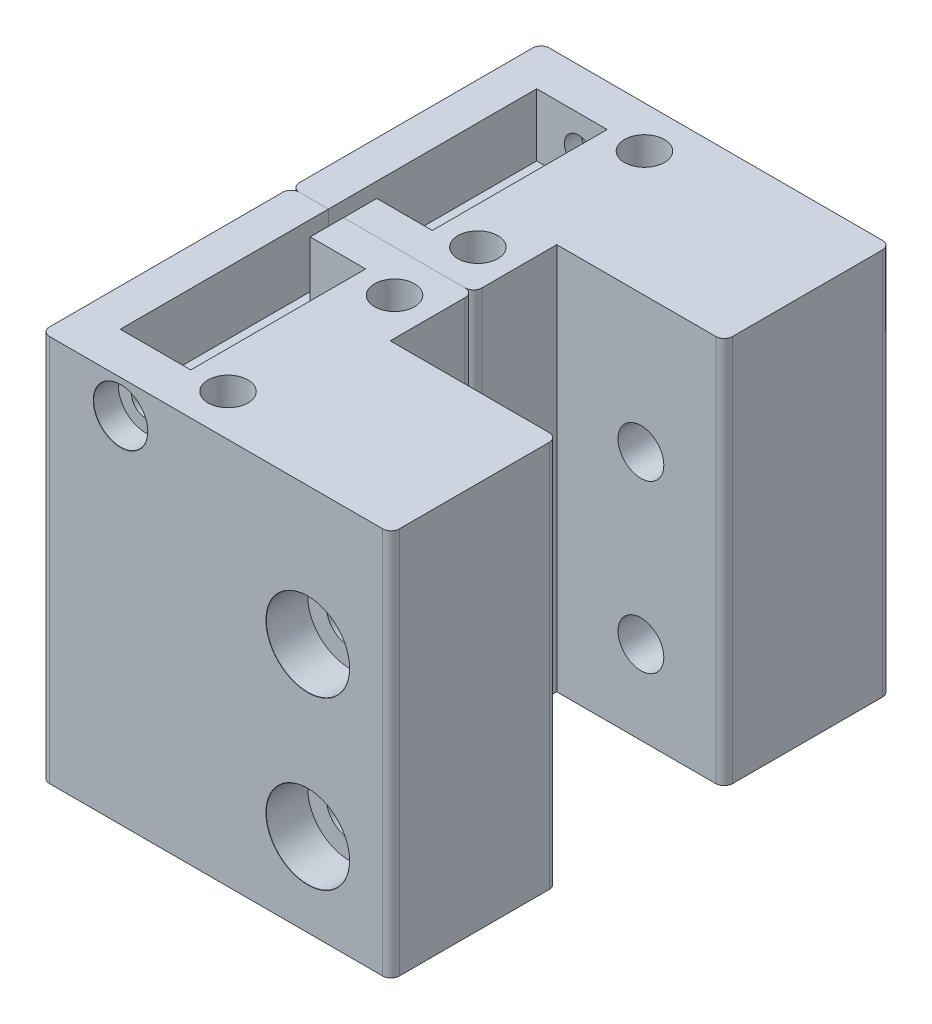
SolidWorks part; units mm, degrees
ref_plane "Front Plane" through (0, 0, 0) normal (0, 0, 1) x (1, 0, 0)
ref_plane "Top Plane" through (0, 0, 0) normal (0, 1, 0) x (1, 0, 0)
ref_plane "Right Plane" through (0, 0, 0) normal (1, 0, 0) x (0, 0, -1)
sketch "Sketch1" plane through (0, 0, 0) normal (0, 1, 0) x (1, 0, 0)
  line L1 (21, 10) -> (-21, 10)
  line L2 (21, 10) -> (21, -10)
  line L3 (21, -10) -> (-21, -10)
  line L4 (-21, 10) -> (-21, -10)
  line L5 (21, 10) -> (-21, -10) construction
  line L6 (21, -10) -> (-21, 10) construction
  point P0 (0, 0)
  dimension "D1" = 20
  dimension "D2" = 42
extrude "Boss-Extrude1" add sketch "Sketch1" along normal blind 40
sketch "Sketch2" plane through (0, 0, 10) normal (0, 0, 1) x (1, 0, 0)
  line L0 (21, 20) -> (-21, 20) construction
  line L3 (21, 40) -> (21, 0) construction
  line L4 (-21, 40) -> (-21, 0) construction
  line L5 (11, 30) -> (11, 10)
  point P9 (11, 20)
  dimension "D1" = 20
  dimension "D2" = 10
hole_wizard "CBORE for M5 SHCS1" positions "Sketch3" profile "Sketch4" counterbore size "M5" standard "ANSI Metric" end condition through all
sketch "Sketch3" plane through (0, 0, 10) normal (0, 0, 1) x (1, 0, 0)
  point P0 (11, 30)
  point P3 (11, 10)
sketch "Sketch4" plane through (11, 30, 10) normal (1, 0, 0) x (0, -1, 0)
  line L0 (0, 0) -> (0, 20)
  line L1 (0, 20) -> (2.75, 20)
  line L3 (2.75, 20) -> (2.75, 5)
  line L4 (5, 5) -> (2.75, 5)
  line L5 (5, 5) -> (5, 0.021)
  line L6 (5, 0.021) -> (5.025, 0)
  line L7 (5.025, 0) -> (0, 0)
  line L8 (-5, 0.021) -> (-5.025, 0) construction
  line L11 (0, -6.35) -> (0, 107.95) construction
  dimension "Thru Hole Dia." = 5.5
  dimension "Thru Hole Depth" = 20
  dimension "C'Bore Dia." = 10
  dimension "C'Bore Depth" = 5
  dimension "Near C'Sink Dia." = 10.05
  dimension "Near C'Sink Angle" = 100
sketch "Sketch5" plane through (0, 40, 0) normal (0, 1, 0) x (1, 0, 0)
  line L4 (-21, 10) -> (-21, -10)
  line L5 (-21, -10) -> (21, -10)
  line L6 (21, -10) -> (21, 10)
  line L7 (21, 10) -> (-21, 10)
  line L8 (-21, 10) -> (-21, -10)
  line L9 (-21, -10) -> (21, -10)
  line L10 (21, -10) -> (21, 10)
  line L11 (21, 10) -> (-21, 10)
  dimension "D1" = 0
extrude "Boss-Extrude2" add sketch "Sketch5" along normal blind 6.5
sketch "Sketch12" plane through (0, 46.5, 0) normal (0, 1, 0) x (1, 0, 0)
  line L0 (21, -10) -> (21, 10) construction
  line L1 (-21, 10) -> (0.9, 10)
  line L2 (-21, 10) -> (-21, 20)
  line L3 (-21, 20) -> (0.9, 20)
  line L4 (0.9, 10) -> (0.9, 20)
  dimension "D1" = 10
  dimension "D2" = 20.1
extrude "Boss-Extrude3" add sketch "Sketch12" against normal up to surface (46.5 mm away) up to face at (0, 0, 0)
sketch "Sketch6" plane through (0, 46.5, 0) normal (0, 1, 0) x (1, 0, 0)
  line L0 (-16.51, 20) -> (-16.51, -5)
  line L2 (-16.51, -5) -> (-8.05, -5)
  line L3 (-8.05, -5) -> (-8.05, 16)
  line L4 (-8.05, 16) -> (-14.71, 16)
  line L5 (-14.71, 16) -> (-14.71, 20)
  line L6 (-21, 20) -> (-21, -10) construction
  line L7 (-16.51, 20) -> (-14.71, 20)
  line L8 (21, -10) -> (-21, -10) construction
  line L9 (0.9, 20) -> (-21, 20) construction
  dimension "D1" = 4.49
  dimension "D2" = 1.8
  dimension "D3" = 5
  dimension "D4" = 8.46
  dimension "D5" = 4
extrude "Cut-Extrude1" cut sketch "Sketch6" against normal blind 7.5
fillet "Fillet1" radius 1 5 edges at (0.9, 23.25, -20) (21, 23.25, 10) (-21, 23.25, -20) (-21, 23.25, 10) (21, 23.25, -10)
sketch "Sketch7" plane through (0, 0, 10) normal (0, 0, 1) x (1, 0, 0)
  circle A0 centre (-11.48, 42.5) radius 1.65 construction
  circle A1 centre (-11.48, 42.5) radius 1.65
hole_wizard "CBORE for M3 SHCS1" positions "Sketch10" profile "Sketch11" counterbore size "M3" standard "ANSI Metric"
sketch "Sketch10" plane through (0, 0, 10) normal (0, 0, 1) x (1, 0, 0)
  point P0 (-11.48, 42.5)
sketch "Sketch11" plane through (-11.48, 42.5, 10) normal (1, 0, 0) x (0, -1, 0)
  line L0 (0, 0) -> (0, 6.0215)
  line L1 (0, 6.0215) -> (1.7, 5)
  line L2 (1.7, 5) -> (1.7, 3)
  line L3 (1.7, 3) -> (3.25, 3)
  line L5 (3.25, 3) -> (3.25, 0.021)
  line L6 (3.25, 0.021) -> (3.275, 0)
  line L7 (3.275, 0) -> (0, 0)
  line L8 (-3.25, 0.021) -> (-3.275, 0) construction
  line L10 (0, 6.0215) -> (-1.7, 5) construction
  line L11 (0, -6.35) -> (0, 107.95) construction
  dimension "Hole Dia." = 3.4
  dimension "Hole Depth" = 5
  dimension "C'Bore Dia." = 6.5
  dimension "C'Bore Depth" = 3
  dimension "Near C'Sink Dia." = 6.55
  dimension "Near C'Sink Angle" = 100
  dimension "Drill Angle" = 118
sketch "Sketch14" plane through (0, 46.5, 0) normal (0, 1, 0) x (1, 0, 0)
  line L0 (-3.575, 20) -> (-3.575, -10) construction
  line L1 (-0.1, 20) -> (-14.71, 20) construction
  line L2 (-20, -10) -> (20, -10) construction
  line L3 (0.9, 10) -> (0.9, 19) construction
  line L4 (-3.575, 15) -> (-3.575, -5) construction
  circle A0 centre (-3.575, 15) radius 2.4
  circle A1 centre (-3.575, -5) radius 2.4
  point P12 (-3.575, 5)
  dimension "D3" = 4.8
  dimension "D1" = 4.475
  dimension "D2" = 20
extrude "Cut-Extrude2" cut sketch "Sketch14" against normal blind 3.8
sketch "Sketch15" plane through (0, 42.7, 0) normal (0, 1, 0) x (1, 0, 0)
  circle A0 centre (-3.575, 15) radius 1.7
  circle A1 centre (-3.575, -5) radius 1.7
  point P0 (-3.575, 15)
  point P1 (-3.575, -5)
  dimension "D1" = 3.4
extrude "Cut-Extrude3" cut sketch "Sketch15" against normal blind 3
mirror "Mirror1" about plane through (-21, -24.0751, -20) normal (0, 0, -1) of bodies 109
